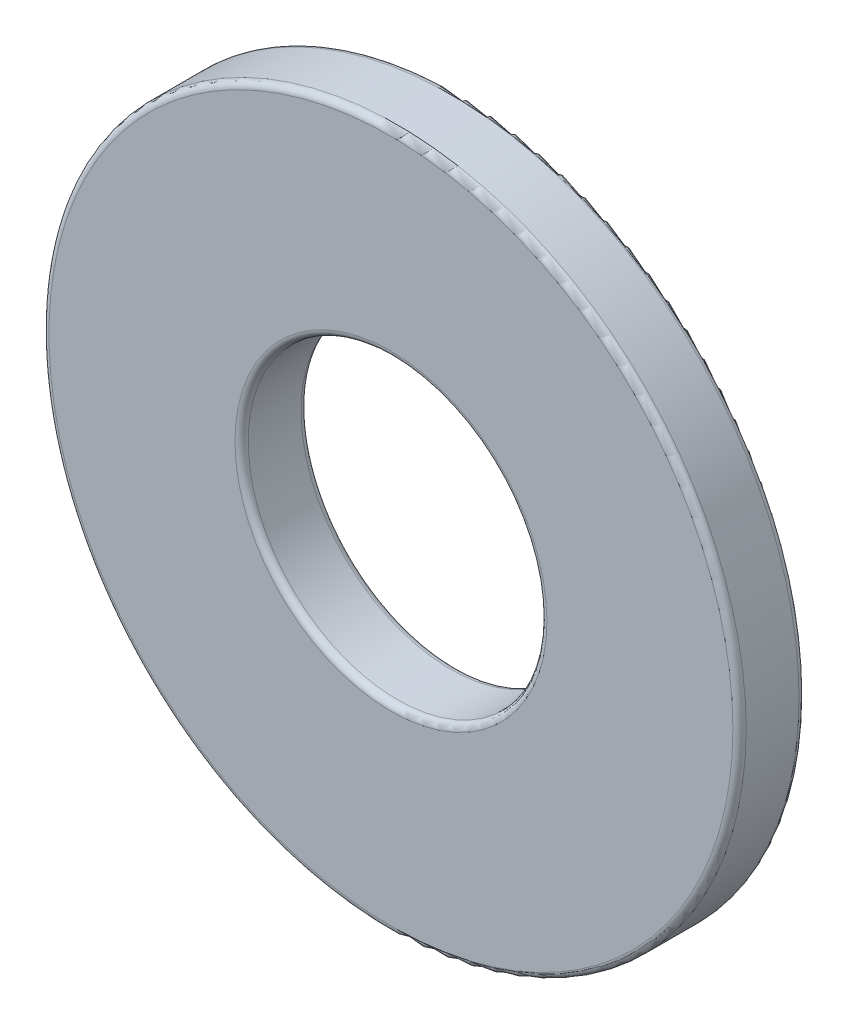
SolidWorks part; units mm, degrees
ref_plane "Front Plane" through (0, 0, 0) normal (0, 0, 1) x (1, 0, 0)
ref_plane "Top Plane" through (0, 0, 0) normal (0, 1, 0) x (1, 0, 0)
ref_plane "Right Plane" through (0, 0, 0) normal (1, 0, 0) x (0, 0, -1)
sketch "Sketch1" plane through (0, 0, 0) normal (0, 0, 1) x (1, 0, 0)
  circle A0 centre (0, 0) radius 11.1125 construction
  circle A1 centre (0, 0) radius 4.7625 construction
  dimension "OD" = 22.225
  dimension "ID" = 9.525
sketch "Sketch2" plane through (0, 0, 0) normal (1, 0, 0) x (0, 0, -1)
  line L0 (-1.0541, -11.1125) -> (1.0541, -11.1125) construction
  point P0 (0.8001, -11.1125)
  point P4 (0, -11.1125)
  dimension "Thickness Max" = 2.1082
  dimension "Thickness Min" = 1.8542
sketch "Sketch3" plane through (0, 0, 0) normal (0, 0, 1) x (1, 0, 0)
  circle A0 centre (0, 0) radius 11.1125 construction
  circle A1 centre (0, 0) radius 11.1125
  circle A2 centre (0, 0) radius 4.7625 construction
  circle A3 centre (0, 0) radius 4.7625
extrude "Boss-Extrude1" add sketch "Sketch3" against normal up to vertex (1.0541 mm away) and the other way up to vertex (1.0541 mm away) up to point (0, -11.1125, -1.0541) other way up to point (0, -11.1125, 1.0541)
fillet "Fillet1" radius 0.2108 4 edges at (11.1125, 0, -1.0541) (4.7625, 0, -1.0541) (4.7625, 0, 1.0541) (11.1125, 0, 1.0541)
equation "\"D1@Fillet1\" = \"Thickness Max@Sketch2\" * 0.1"
